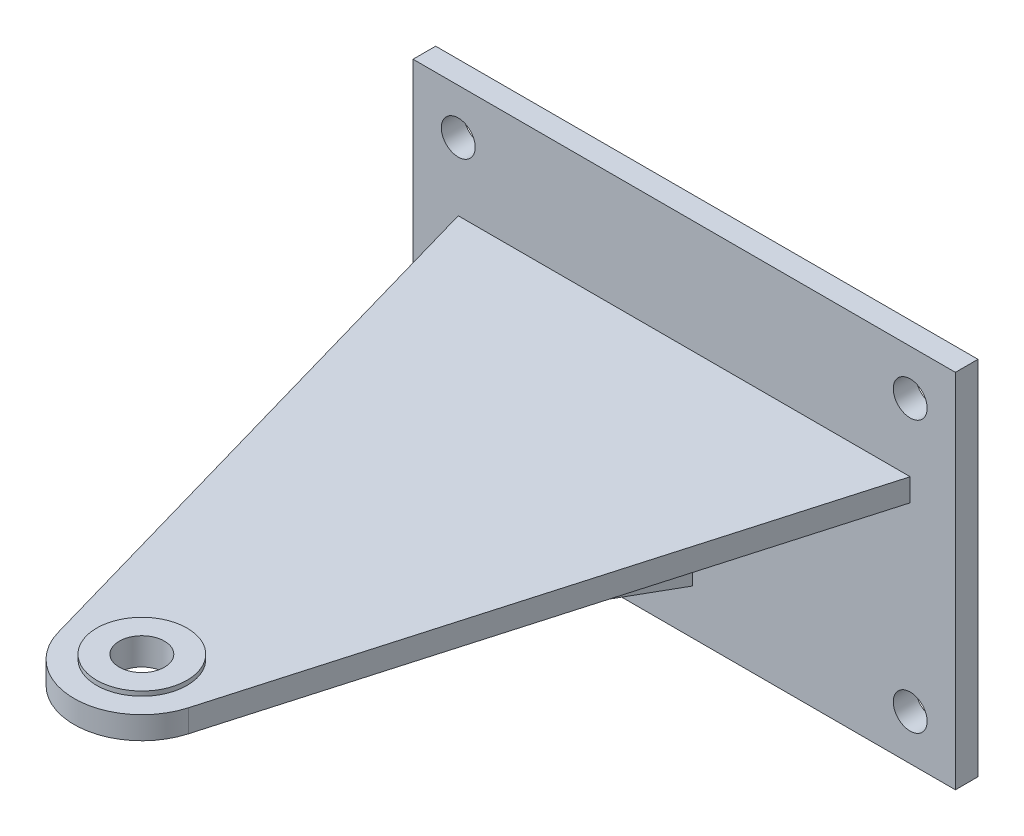
SolidWorks part; units mm, degrees
material "ABS"
ref_plane "Front Plane" through (0, 0, 0) normal (0, 0, 1) x (1, 0, 0)
ref_plane "Top Plane" through (0, 0, 0) normal (0, 1, 0) x (1, 0, 0)
ref_plane "Right Plane" through (0, 0, 0) normal (1, 0, 0) x (0, 0, -1)
sketch "Sketch1" plane through (0, 0, 0) normal (0, 0, 1) x (1, 0, 0)
  line L1 (76.2, -50.8) -> (-76.2, -50.8)
  line L2 (76.2, -50.8) -> (76.2, 50.8)
  line L3 (76.2, 50.8) -> (-76.2, 50.8)
  line L4 (-76.2, -50.8) -> (-76.2, 50.8)
  line L5 (76.2, -50.8) -> (-76.2, 50.8) construction
  line L6 (76.2, 50.8) -> (-76.2, -50.8) construction
  point P0 (0, 0)
  dimension "D1" = 152.4
  dimension "D2" = 101.6
extrude "Boss-Extrude1" add sketch "Sketch1" along normal blind 6.35
ref_plane "Plane1" through (0, 19.05, 0) normal (0, 1, 0) x (1, 0, 0)
sketch "Sketch4" plane through (0, 19.05, 0) normal (0, 1, 0) x (1, 0, 0)
  line L0 (0, 0) -> (0, -80.788) construction
  line L1 (63.5, -6.35) -> (18.3126, -163.999)
  line L2 (76.2, -6.35) -> (-76.2, -6.35) construction
  line L3 (-63.5, -6.35) -> (-18.3126, -163.999)
  line L4 (-63.5, -6.35) -> (63.5, -6.35)
  arc A0 (18.3126, -163.999) -> (-18.3126, -163.999) centre (0, -158.75) cw
  point P10 (0, -6.35)
  dimension "D2" = 19.05
  dimension "D1" = 127
  dimension "D3" = 152.4
extrude "Boss-Extrude2" add sketch "Sketch4" against normal blind 6.35
sketch "Sketch5" plane through (0, 19.05, 0) normal (0, 1, 0) x (1, 0, 0)
  circle A0 centre (0, -158.75) radius 12.7
  dimension "D1" = 25.4
extrude "Boss-Extrude3" add sketch "Sketch5" along normal blind 1.27
sketch "Sketch6" plane through (0, 0, 0) normal (1, 0, 0) x (0, 0, -1)
  line L0 (-6.35, -38.1) -> (-146.05, 12.7)
  line L1 (-6.35, -50.8) -> (-6.35, 50.8) construction
  line L2 (-163.999, 12.7) -> (-6.35, 12.7) construction
  line L3 (-6.35, 12.7) -> (-146.05, 12.7)
  line L4 (-6.35, 12.7) -> (-6.35, -38.1)
  dimension "D1" = 139.7
  dimension "D2" = 50.8
extrude "Boss-Extrude4" add sketch "Sketch6" along normal mid plane 4.7625
ref_plane "Plane2" through (25.4, 0, 0) normal (1, 0, 0) x (0, 0, -1)
sketch "Sketch7" plane through (25.4, 0, 0) normal (1, 0, 0) x (0, 0, -1)
  line L0 (-57.15, 12.7) -> (-6.35, -12.7)
  line L1 (-6.35, 12.7) -> (-146.05, 12.7) construction
  line L2 (-6.35, -50.8) -> (-6.35, 50.8) construction
  dimension "D1" = 50.8
  dimension "D2" = 25.4
rib "Rib1" sketch "Sketch7" sketch "Sketch7" thickness 2.54 extrusion direction parallel to sketch draft on no parameters "D1"=2.54
mirror "Mirror1" about plane through (0, 0, 0) normal (1, 0, 0) of "Rib1"
sketch "Sketch8" plane through (0, 20.32, 0) normal (0, 1, 0) x (1, 0, 0)
  circle A0 centre (0, -158.75) radius 6.35
  dimension "D1" = 12.7
extrude "Cut-Extrude1" cut sketch "Sketch8" against normal through all
sketch "Sketch9" plane through (0, 0, 6.35) normal (0, 0, 1) x (1, 0, 0)
  line L0 (-76.2, 50.8) -> (-76.2, -50.8) construction
  line L1 (76.2, 50.8) -> (-76.2, 50.8) construction
  circle A0 centre (-63.5, 38.1) radius 4.7625
  dimension "D1" = 9.525
  dimension "D2" = 12.7
  dimension "D3" = 12.7
extrude "Cut-Extrude2" cut sketch "Sketch9" against normal through all both and the other way through all
pattern_linear "LPattern1" count 2 spacing 127 along (1, 0, 0) count 2 spacing 76.2 along (0, -1, 0) of "Cut-Extrude2"
